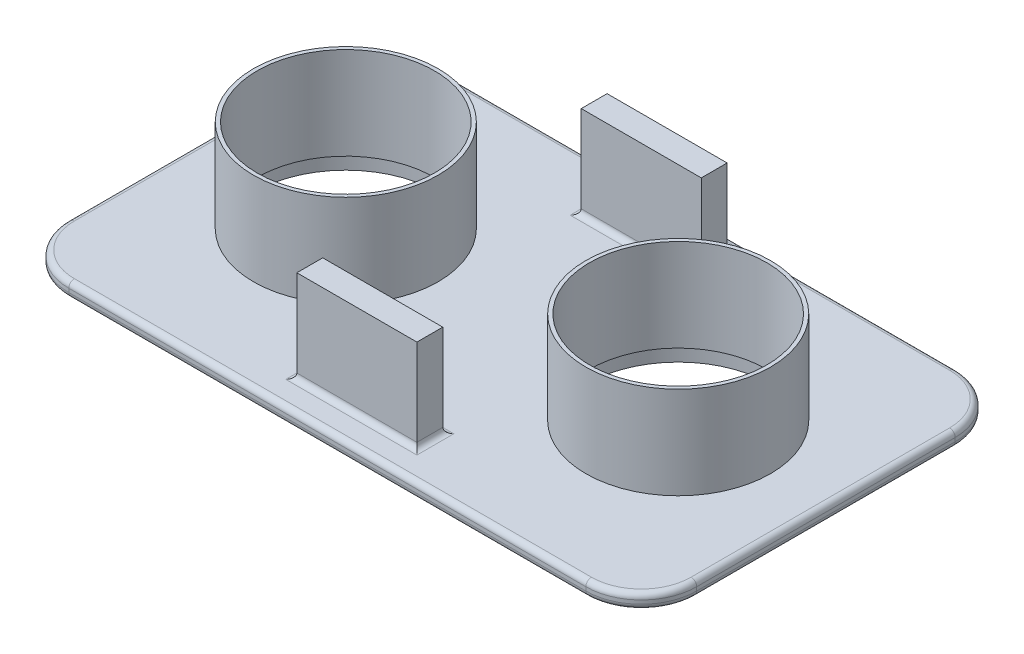
SolidWorks part; units mm, degrees
material "1060 Alloy"
ref_plane "Front Plane" through (0, 0, 0) normal (0, 0, 1) x (1, 0, 0)
ref_plane "Top Plane" through (0, 0, 0) normal (0, 1, 0) x (1, 0, 0)
ref_plane "Right Plane" through (0, 0, 0) normal (1, 0, 0) x (0, 0, -1)
sketch "Sketch1" plane through (0, 0, 0) normal (0, 1, 0) x (1, 0, 0)
  line L0 (-281.8898, 0) -> (259.5299, 0) construction
  line L1 (-140, 100) -> (140, 100)
  line L2 (-170, 70) -> (-170, -70)
  line L3 (-140, -100) -> (140, -100)
  line L4 (170, 70) -> (170, -70)
  line L5 (-170, 100) -> (170, -100) construction
  line L6 (-170, -100) -> (170, 100) construction
  line L7 (0, -144.2371) -> (0, 106.3228) construction
  arc A1 (-170, -70) -> (-140, -100) centre (-140, -70) ccw
  arc A2 (140, -100) -> (170, -70) centre (140, -70) ccw
  arc A3 (140, 100) -> (170, 70) centre (140, 70) cw
  arc A4 (-140, 100) -> (-170, 70) centre (-140, 70) ccw
  circle A5 centre (-90, 0) radius 50
  circle A6 centre (90, 0) radius 50
  point P0 (0, 0)
  dimension "D4" = 30
  dimension "D3" = 100
  dimension "D1" = 340
  dimension "D2" = 200
  dimension "D5" = 40
extrude "Boss-Extrude1" add sketch "Sketch1" along normal blind 8
ref_plane "Plane1" through (0, 50, 0) normal (0, 1, 0) x (1, 0, 0)
sketch "Sketch2" plane through (0, 8, 0) normal (0, 1, 0) x (1, 0, 0)
  line L0 (-191.1959, 0) -> (191.1959, 0) construction
  line L1 (0, -113.7921) -> (0, 114.2127) construction
  line L2 (-32.5, -70) -> (32.5, -70)
  line L3 (-32.5, 84) -> (32.5, 84)
  line L4 (-32.5, 84) -> (-32.5, 70)
  line L5 (-32.5, 70) -> (32.5, 70)
  line L6 (32.5, 84) -> (32.5, 70)
  line L7 (-32.5, 84) -> (32.5, 70) construction
  line L8 (-32.5, 70) -> (32.5, 84) construction
  line L9 (32.5, -84) -> (32.5, -70)
  line L10 (-32.5, -84) -> (32.5, -84)
  line L11 (-32.5, -84) -> (-32.5, -70)
  circle A0 centre (-90, 0) radius 50
  circle A1 centre (90, 0) radius 50
  point P5 (0, 77)
  dimension "D5" = 100
  dimension "D1" = 65
  dimension "D2" = 14
  dimension "D3" = 70
  dimension "D4" = 40
extrude "Boss-Extrude2" add sketch "Sketch2" along normal blind 50
sketch "Sketch4" plane through (0, 58, 0) normal (0, 1, 0) x (1, 0, 0)
  line L0 (-207.1815, 0) -> (206.3401, 0) construction
  line L1 (0, -134.8257) -> (0, 119.6815) construction
  circle A0 centre (-90, 0) radius 48
  circle A2 centre (90, 0) radius 48
  dimension "D1" = 42
extrude "Cut-Extrude1" cut sketch "Sketch4" against normal through all
fillet "Fillet2" radius 3 8 edges at (-32.5, 8, 77) (0, 8, 84) (0, 8, 70) (32.5, 8, -77) (0, 8, -84) (-32.5, 8, -77) (0, 8, -70) (32.5, 8, 77)
fillet "Fillet3" radius 3 16 edges at (-161.2132, 0, 91.2132) (-170, 0, 0) (-161.2132, 0, -91.2132) (0, 0, -100) (161.2132, 0, -91.2132) (170, 0, 0) (161.2132, 0, 91.2132) (-161.2132, 8, 91.2132) (-170, 8, 0) (-161.2132, 8, -91.2132) (0, 8, -100) (161.2132, 8, -91.2132) (170, 8, 0) (161.2132, 8, 91.2132) (0, 0, 100) (0, 8, 100)
equation "\"heave-th-place\"=100"
equation "\"D3@Sketch1\"=\"heave-th-place\""
equation "\"D5@Sketch2\"=\"heave-th-place\""
